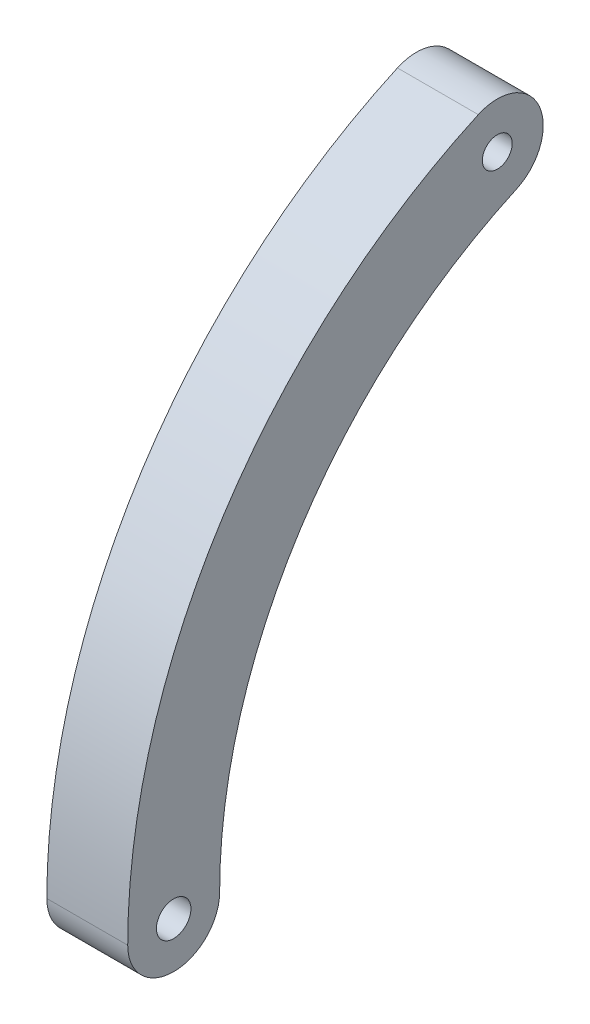
SolidWorks part; units mm, degrees
material "ABS"
ref_plane "Front Plane" through (0, 0, 0) normal (0, 0, 1) x (1, 0, 0)
ref_plane "Top Plane" through (0, 0, 0) normal (0, 1, 0) x (1, 0, 0)
ref_plane "Right Plane" through (0, 0, 0) normal (1, 0, 0) x (0, 0, -1)
sketch "Esquisse1" plane through (0, 0, 0) normal (1, 0, 0) x (0, 0, -1)
  arc A0 (-34.925, 0) -> (-14.4308, 31.8042) centre (0, 0) cw
  arc A1 (-41.275, 0) -> (-17.0546, 37.5868) centre (0, 0) cw
  arc A2 (-41.275, 0) -> (-34.925, 0) centre (-38.1, 0) ccw
  arc A3 (-14.4308, 31.8042) -> (-17.0546, 37.5868) centre (-15.7427, 34.6955) ccw
  circle A4 centre (-38.1, 0) radius 1.1906
  circle A5 centre (-15.7427, 34.6955) radius 1.0319
  dimension "D1" = 3.175
  dimension "D4" = 2.3812
  dimension "D5" = 2.0638
  dimension "D2" = 41.275
  dimension "D3" = 38.1
extrude "Boss.-Extru.1" add sketch "Esquisse1" along normal blind 5.588
